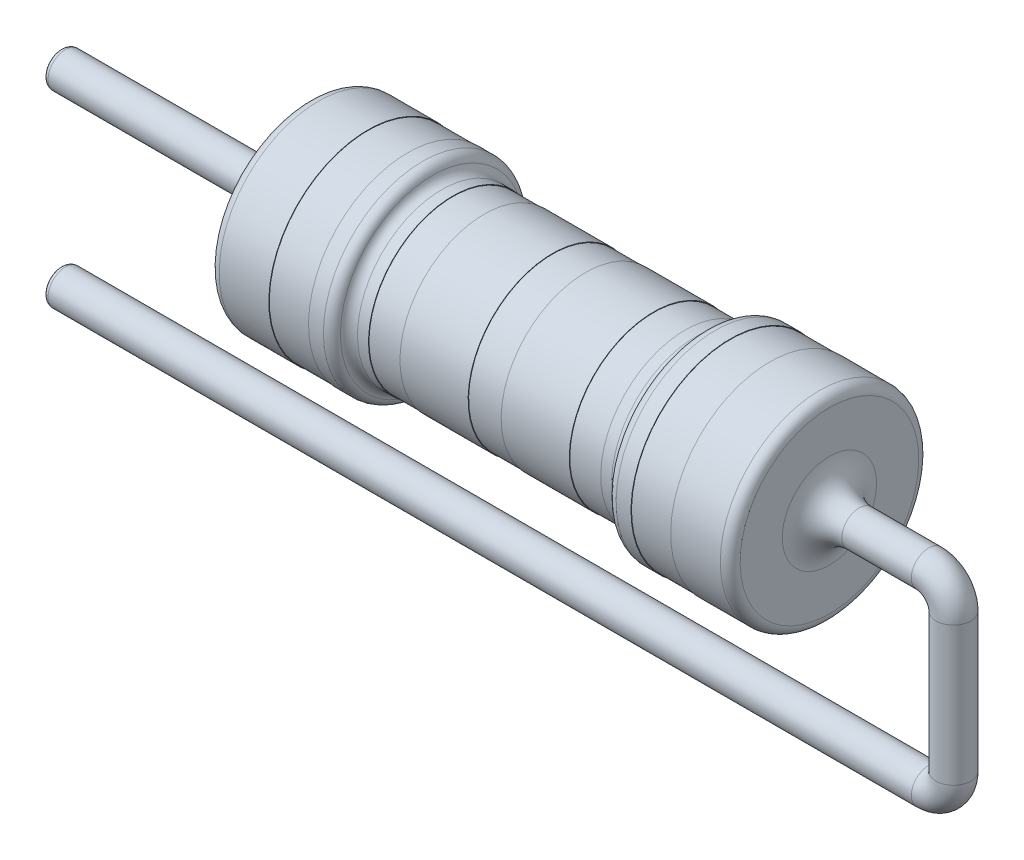
SolidWorks part; units mm, degrees
ref_plane "Front Plane" through (0, 0, 0) normal (0, 0, 1) x (1, 0, 0)
ref_plane "Top Plane" through (0, 0, 0) normal (0, 1, 0) x (1, 0, 0)
ref_plane "Right Plane" through (0, 0, 0) normal (1, 0, 0) x (0, 0, -1)
sketch "Sketch1" plane through (0, 0, 0) normal (0, 0, 1) x (1, 0, 0)
  line L0 (-5.25, 0) -> (5.25, 0)
  line L1 (5.25, 0) -> (5.25, -2)
  line L2 (5.25, -2) -> (4.05, -2)
  line L4 (4.05, -2) -> (4.05, -1.99)
  line L5 (4.05, -1.99) -> (3.25, -1.99)
  line L6 (3.25, -1.99) -> (3.25, -2)
  line L7 (3.25, -2) -> (2.75, -2)
  line L8 (2.75, -2) -> (2.75, -1.7)
  line L9 (2.75, -1.7) -> (2.3407, -1.7)
  line L10 (2.3407, -1.7) -> (2.3407, -1.69)
  line L11 (2.3407, -1.69) -> (1.7068, -1.69)
  line L12 (1.7068, -1.69) -> (1.7068, -1.7)
  line L13 (1.7068, -1.7) -> (0.3325, -1.7)
  line L14 (0.3325, -1.7) -> (0.3325, -1.69)
  line L15 (0.3325, -1.69) -> (-0.3325, -1.69)
  line L16 (-0.3325, -1.7) -> (-0.3325, -1.69)
  line L17 (-1.7068, -1.7) -> (-0.3325, -1.7)
  line L18 (-1.7068, -1.69) -> (-1.7068, -1.7)
  line L19 (-2.3407, -1.69) -> (-1.7068, -1.69)
  line L20 (-2.3407, -1.7) -> (-2.3407, -1.69)
  line L21 (-2.75, -1.7) -> (-2.3407, -1.7)
  line L22 (-2.75, -2) -> (-2.75, -1.7)
  line L23 (-3.25, -2) -> (-2.75, -2)
  line L24 (-3.25, -1.99) -> (-3.25, -2)
  line L25 (-4.05, -1.99) -> (-3.25, -1.99)
  line L26 (-4.05, -2) -> (-4.05, -1.99)
  line L27 (-5.25, -2) -> (-4.05, -2)
  line L28 (-5.25, 0) -> (-5.25, -2)
  point P20 (0, -1.69)
  point P33 (0, 0)
  dimension "D2" = 2.5
  dimension "D3" = 0.8
  dimension "D4" = 1.2
  dimension "D5" = 0.3
  dimension "D6" = 0.01
  dimension "D7" = 0.01
  dimension "D8" = 0.01
revolve "Revolve1" add sketch "Sketch1" angle 360 about L0
sketch "Sketch2" plane through (5.25, 0, 0) normal (1, 0, 0) x (0, 0, -1)
  circle A0 centre (0, 0) radius 0.4
fillet "Fillet2" radius 0.2 1 edges at (-2.75, -2, 0)
fillet "Fillet3" radius 0.2 2 edges at (-2.75, -1.7, 0) (2.75, -2, 0)
fillet "Fillet4" radius 0.2 1 edges at (2.75, -1.7, 0)
fillet "Fillet5" radius 0.2 1 edges at (-5.25, -2, 0)
fillet "Fillet6" radius 0.2 1 edges at (5.25, -2, 0)
ref_plane "Plane2" [suppressed] through (5.25, 0, 0) normal (1, 0, 0) x (0, 0, -1)
sketch3d "3DSketch7" [suppressed]
  line L0 (5.25, 0, 0) -> (7.75, 0, 0)
  line L1 (8.75, -1, 0) -> (8.75, -6, 0)
  arc A0 (7.75, 0, 0) -> (8.75, -1, 0) centre (7.75, -1, 0) ccw
  point P6 (8.75, 0, 0)
  point P7 (7.75, -1, -1)
  dimension "D3" = 1
  dimension "D1" = 3.5
  dimension "D2" = 6
sweep "Sweep3" [suppressed] add profiles "Sketch2" path "3DSketch7"
mirror "Mirror3" [suppressed] about plane through (0, 0, 0) normal (1, 0, 0)
fillet "Fillet12" [suppressed] radius 0.1
fillet "Fillet13" [suppressed] radius 0.8
fillet "Fillet14" [suppressed] radius 0.8
sketch "Sketch3" plane through (5.25, 0, 0) normal (1, 0, 0) x (0, 0, -1)
  circle A0 centre (0, 0) radius 0.35
sketch3d "3DSketch8"
  line L0 (5.25, 0, 0) -> (7.25, 0, 0)
  line L1 (7.75, -0.5, 0) -> (7.75, -3.2963, 0)
  line L2 (7.25, -3.7963, 0) -> (-10.25, -3.7963, 0)
  arc A0 (7.75, -0.5, 0) -> (7.25, 0, 0) centre (7.25, -0.5, 0) ccw
  arc A1 (7.25, -3.7963, 0) -> (7.75, -3.2963, 0) centre (7.25, -3.2963, 0) ccw
  point P6 (7.75, 0, 0)
  point P7 (7.25, -0.5, 0.5)
  point P11 (7.75, -3.7963, 0)
  point P12 (7.25, -3.2963, 0.5)
  dimension "D2" = 0.5
  dimension "D4" = 0.5
  dimension "D1" = 2.5
  dimension "D3" = 18
sketch3d "3DSketch9" plane through (0, 0, 0) normal (0, 0, 1) x (1, 0, 0)
sweep "Sweep5" add profiles "Sketch3" path "3DSketch8"
sketch "Sketch4" plane through (-5.25, 0, 0) normal (-1, 0, 0) x (0, 0, 1)
  circle A0 centre (0, 0) radius 0.35
sketch3d "3DSketch12"
  line L0 (-5.25, 0, 0) -> (-10.25, 0, 0)
  dimension "D1" = 5
sweep "Sweep6" add profiles "Sketch4" path "3DSketch12"
fillet "Fillet17" radius 0.1 2 edges at (-10.25, -4.1463, 0) (-10.25, -0.35, 0)
fillet "Fillet18" radius 0.6 2 edges at (5.25, 0.35, 0) (-5.25, -0.35, 0)
